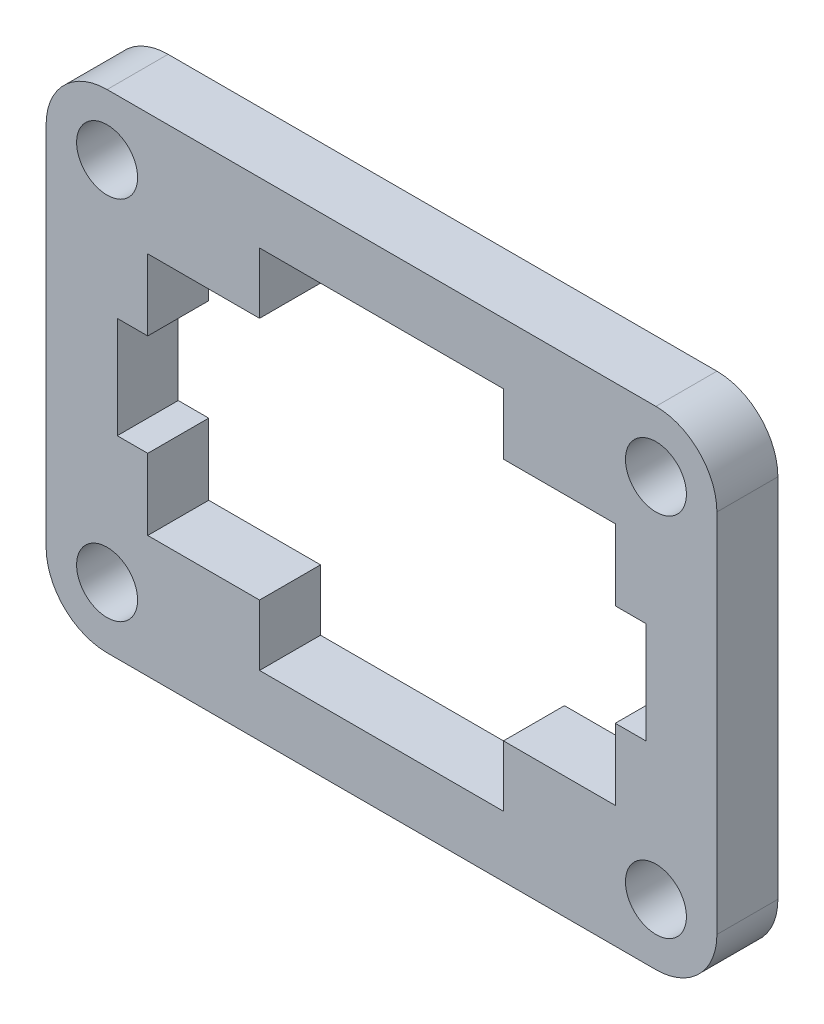
SolidWorks part; units mm, degrees
ref_plane "Plan de face" through (0, 0, 0) normal (0, 0, 1) x (1, 0, 0)
ref_plane "Plan de dessus" through (0, 0, 0) normal (0, 1, 0) x (1, 0, 0)
ref_plane "Plan de droite" through (0, 0, 0) normal (1, 0, 0) x (0, 0, -1)
sketch "Esquisse16" plane through (0, 0, 0) normal (0, 0, 1) x (1, 0, 0)
  line L1 (27.0303, -10.6514) -> (54.0303, -10.6514)
  line L2 (24.0303, -13.6514) -> (24.0303, -31.6514)
  line L3 (27.0303, -34.6514) -> (54.0303, -34.6514)
  line L4 (57.0303, -13.6514) -> (57.0303, -31.6514)
  line L5 (29.0303, -28.6514) -> (34.5303, -28.6514)
  line L6 (29.0303, -28.6514) -> (29.0303, -25.1514)
  line L7 (29.0303, -16.6514) -> (34.5303, -16.6514)
  line L8 (52.0303, -28.6514) -> (52.0303, -25.1514)
  line L9 (46.5303, -31.6514) -> (34.5303, -31.6514)
  line L10 (46.5303, -31.6514) -> (46.5303, -28.6514)
  line L11 (46.5303, -13.6514) -> (34.5303, -13.6514)
  line L12 (34.5303, -31.6514) -> (34.5303, -28.6514)
  line L13 (27.5303, -20.1514) -> (29.0303, -20.1514)
  line L14 (27.5303, -20.1514) -> (27.5303, -25.1514)
  line L15 (27.5303, -25.1514) -> (29.0303, -25.1514)
  line L16 (53.5303, -20.1514) -> (53.5303, -25.1514)
  line L17 (29.0303, -20.1514) -> (29.0303, -16.6514)
  line L20 (46.5303, -28.6514) -> (52.0303, -28.6514)
  line L22 (52.0303, -25.1514) -> (53.5303, -25.1514)
  line L23 (52.0303, -20.1514) -> (52.0303, -16.6514)
  line L24 (52.0303, -20.1514) -> (53.5303, -20.1514)
  line L25 (46.5303, -16.6514) -> (46.5303, -13.6514)
  line L26 (46.5303, -16.6514) -> (52.0303, -16.6514)
  line L27 (34.5303, -16.6514) -> (34.5303, -13.6514)
  arc A0 (24.0303, -31.6514) -> (27.0303, -34.6514) centre (27.0303, -31.6514) ccw
  arc A1 (54.0303, -34.6514) -> (57.0303, -31.6514) centre (54.0303, -31.6514) ccw
  arc A2 (54.0303, -10.6514) -> (57.0303, -13.6514) centre (54.0303, -13.6514) cw
  arc A3 (27.0303, -10.6514) -> (24.0303, -13.6514) centre (27.0303, -13.6514) ccw
  circle A4 centre (27.0303, -13.6514) radius 1.5
  circle A5 centre (54.0303, -13.6514) radius 1.5
  circle A6 centre (54.0303, -31.6514) radius 1.5
  circle A7 centre (27.0303, -31.6514) radius 1.5
  point P22 (24.0303, -34.6514)
  point P31 (57.0303, -10.6514)
  point P34 (24.0303, -10.6514)
  dimension "D15" = 3
  dimension "D16" = 3
  dimension "D17" = 3
  dimension "D18" = 3
  dimension "D19" = 3
  dimension "D2" = 33
  dimension "D3" = 12
  dimension "D4" = 12
  dimension "D5" = 6
  dimension "D6" = 10.5
  dimension "D7" = 3
  dimension "D8" = 3
  dimension "D9" = 5
  dimension "D10" = 5
  dimension "D11" = 3.5
  dimension "D12" = 3.5
  dimension "D13" = 3.5
  dimension "D14" = 3.5
  dimension "D20" = 3
extrude "Boss.-Extru.16" add sketch "Esquisse16" along normal blind 3 separate body
